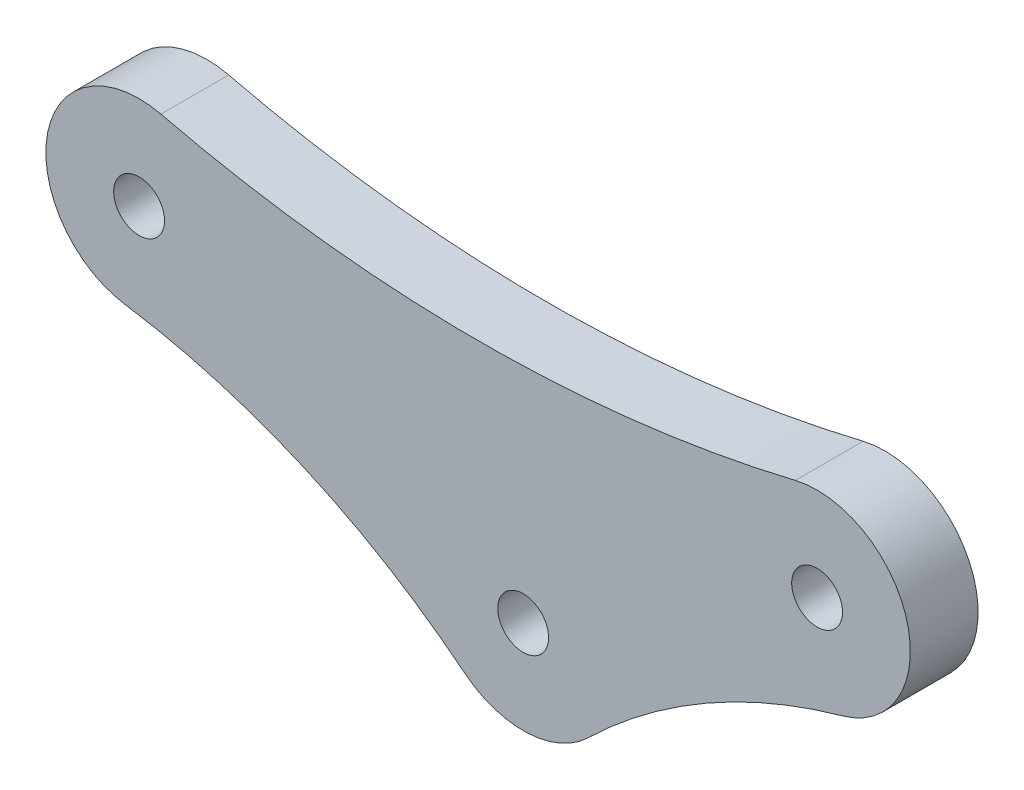
SolidWorks part; units mm, degrees
ref_plane "Front Plane" through (0, 0, 0) normal (0, 0, 1) x (1, 0, 0)
ref_plane "Top Plane" through (0, 0, 0) normal (0, 1, 0) x (1, 0, 0)
ref_plane "Right Plane" through (0, 0, 0) normal (1, 0, 0) x (0, 0, -1)
sketch "Sketch1" plane through (0, 0, 0) normal (0, 0, 1) x (1, 0, 0)
  line L0 (0, 0) -> (-17.34, -9.9662) construction
  circle A0 centre (0, 0) radius 1.5
  circle A1 centre (-17.34, -9.9662) radius 1.5
  circle A2 centre (-40, 0) radius 1.5
  circle A3 centre (-40, 0) radius 5.5
  circle A4 centre (-17.34, -9.9662) radius 5.5
  circle A5 centre (0, 0) radius 5.5
  arc A6 (-38.7135, 5.3474) -> (-1.2865, 5.3474) centre (-20, 83.1279) ccw
  arc A7 (-40.8259, -5.4376) -> (-20.7897, -14.2498) centre (-47.1326, -46.9614) cw
  arc A8 (-13.51, -13.9134) -> (1.4827, -5.2964) centre (10.9535, -39.1257) cw
  point P19 (-40.2237, 2.1396)
  point P20 (-41.0082, -0.9985)
  point P21 (0, 0)
  point P22 (-40.8628, 0)
  point P23 (0, 0)
  dimension "D1" = 3
  dimension "D2" = 4
  dimension "D6" = 80
  dimension "D7" = 42
  dimension "D8" = 35.13
  dimension "D3" = 20
  dimension "D4" = 17.34
  dimension "D5" = 40
extrude "Boss-Extrude1" add sketch "Sketch1" along normal blind 4
